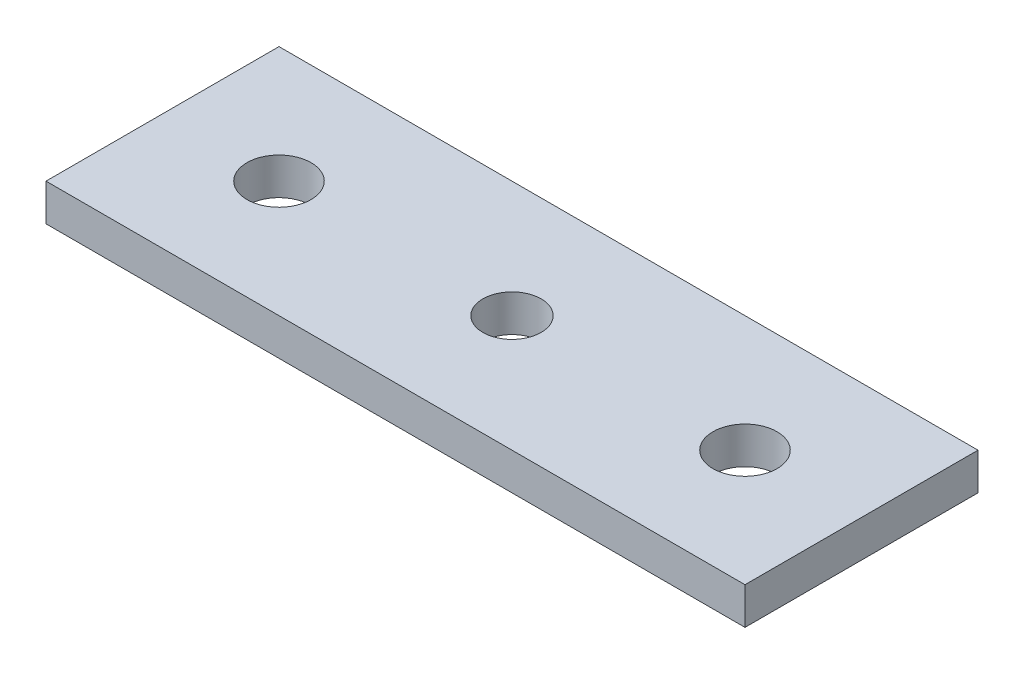
SolidWorks part; units mm, degrees
ref_plane "Front Plane" through (0, 0, 0) normal (0, 0, 1) x (1, 0, 0)
ref_plane "Top Plane" through (0, 0, 0) normal (0, 1, 0) x (1, 0, 0)
ref_plane "Right Plane" through (0, 0, 0) normal (1, 0, 0) x (0, 0, -1)
sketch "Sketch1" plane through (0, 0, 0) normal (0, 1, 0) x (1, 0, 0)
  line L0 (0, 10) -> (60, 10) construction
  line L1 (0, 0) -> (60, 0)
  line L2 (0, 0) -> (0, 20)
  line L3 (0, 20) -> (60, 20)
  line L4 (60, 0) -> (60, 20)
  line L5 (30, 0) -> (30, 20) construction
  point P9 (10, 10)
  point P10 (50, 10)
  dimension "D1" = 20
  dimension "D2" = 60
  dimension "D3" = 20
extrude "Boss-Extrude1" add sketch "Sketch1" along normal blind 3.175
sketch "Sketch4" plane through (0, 0, 0) normal (0, -1, 0) x (1, 0, 0)
  circle A0 centre (50, -10) radius 2.75
  circle A1 centre (10, -10) radius 2.75
  point P0 (10, -10)
  point P2 (50, -10)
  dimension "D1" = 5.5
  dimension "D2" = 5.5
extrude "Cut-Extrude1" cut sketch "Sketch4" against normal blind 3.175 contours A0 | A1
sketch "Sketch5" plane through (0, 0, 0) normal (0, -1, 0) x (-1, 0, 0)
  line L0 (0, 10) -> (-60, 10) construction
  point P0 (-30, 10)
hole_wizard "M6x1.0 Tapped Hole1" positions "3DSketch1" profile "Sketch6" tap size "M6x1.0" standard "ANSI Metric" end condition through all
sketch3d "3DSketch1"
  point P0 (30, 0, -10)
sketch "Sketch6" plane through (30, 0, -10) normal (1, 0, 0) x (0, 0, -1)
  line L0 (0, 0) -> (0, 3.175)
  line L1 (0, 3.175) -> (2.5, 3.175)
  line L2 (2.5, 3.175) -> (2.5, 0)
  line L5 (2.5, 0) -> (0, 0)
  line L11 (0, -6.35) -> (0, 107.95) construction
  dimension "Thru Tap Drill Dia." = 5
  dimension "Thru Tap Drill Depth" = 3.175
cosmetic thread "Hole Thread1" parameters "D2"=6
